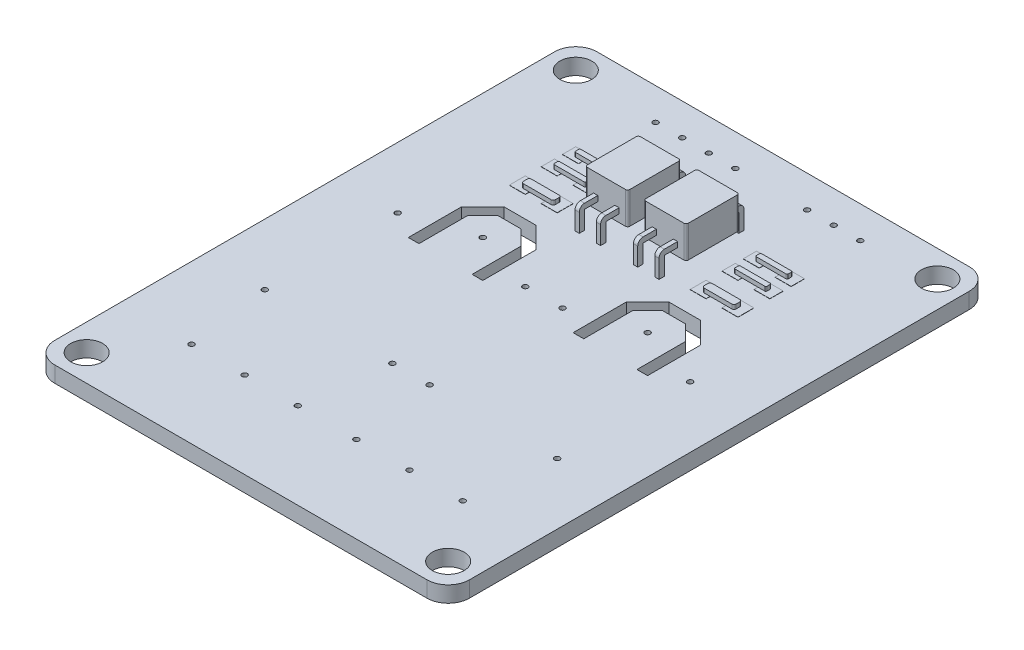
SolidWorks part; units mm, degrees
ref_plane "Ön Düzlem" through (0, 0, 0) normal (0, 0, 1) x (1, 0, 0)
ref_plane "Üst Düzlem" through (0, 0, 0) normal (0, 1, 0) x (1, 0, 0)
ref_plane "Sağ Düzlem" through (0, 0, 0) normal (1, 0, 0) x (0, 0, -1)
sketch "Çizim1" plane through (0, 0, 0) normal (0, 1, 0) x (1, 0, 0)
  line L0 (0, 0) -> (0, 25.5) construction
  line L1 (-17.5, 25.5) -> (17.5, 25.5)
  line L2 (-19.5, 23.5) -> (-19.5, -23.5)
  line L3 (-17.5, -25.5) -> (17.5, -25.5)
  line L4 (19.5, 23.5) -> (19.5, -23.5)
  line L5 (-19.5, 25.5) -> (19.5, -25.5) construction
  line L6 (-19.5, -25.5) -> (19.5, 25.5) construction
  line L7 (0, 25.5) -> (0, 0) construction
  line L8 (0, 0) -> (19.5, 0) construction
  line L9 (-13.75, 25.5) -> (-13.75, -25.5) construction
  line L10 (-19.5, -9.5) -> (19.5, -9.5) construction
  line L11 (-19.5, 3) -> (19.5, 3) construction
  line L12 (-1.75, 25.5) -> (-1.75, -25.5) construction
  line L13 (-19.5, 5) -> (19.5, 5) construction
  line L14 (-7.75, 5) -> (-7.75, -25.5) construction
  line L15 (-19.5, -17.39) -> (19.5, -17.39) construction
  line L16 (-11.25, 6.5) -> (-9.25, 8.5)
  line L17 (-9.25, 8.5) -> (-6.25, 8.5)
  line L18 (-11.25, 6.5) -> (-11.25, 1.5)
  line L20 (-4.25, 6.5) -> (-4.25, 1.5)
  line L21 (-11.25, 8.5) -> (-4.25, 1.5) construction
  line L22 (-11.25, 1.5) -> (-4.25, 8.5) construction
  line L24 (-5.25, 6.0858) -> (-5.25, 1.5)
  line L26 (-8.8358, 7.5) -> (-6.6642, 7.5)
  line L27 (-10.25, 6.0858) -> (-8.8358, 7.5)
  line L28 (-10.25, 6.0858) -> (-10.25, 1.5)
  line L30 (-11.25, 1.5) -> (-10.25, 1.5)
  line L31 (-5.25, 1.5) -> (-4.25, 1.5)
  line L32 (-6.25, 8.5) -> (-4.25, 6.5)
  line L33 (-6.6642, 7.5) -> (-5.25, 6.0858) construction
  line L34 (-6.25, 8.5) -> (-4.25, 6.5) construction
  line L35 (-6.6642, 7.5) -> (-5.25, 6.0858)
  line L36 (5.25, 1.5) -> (4.25, 1.5)
  line L37 (4.25, 6.5) -> (4.25, 1.5)
  line L38 (5.25, 6.0858) -> (5.25, 1.5)
  line L39 (6.6642, 7.5) -> (5.25, 6.0858)
  line L40 (6.25, 8.5) -> (4.25, 6.5)
  line L41 (8.8358, 7.5) -> (6.6642, 7.5)
  line L42 (9.25, 8.5) -> (6.25, 8.5)
  line L43 (10.25, 6.0858) -> (8.8358, 7.5)
  line L44 (11.25, 6.5) -> (9.25, 8.5)
  line L45 (10.25, 6.0858) -> (10.25, 1.5)
  line L46 (11.25, 6.5) -> (11.25, 1.5)
  line L47 (11.25, 1.5) -> (10.25, 1.5)
  line L48 (-19.5, 22.5) -> (19.5, 22.5) construction
  line L49 (7.75, 5) -> (7.75, 25.5) construction
  arc A0 (17.5, -25.5) -> (19.5, -23.5) centre (17.5, -23.5) ccw
  arc A1 (-19.5, -23.5) -> (-17.5, -25.5) centre (-17.5, -23.5) ccw
  arc A2 (17.5, 25.5) -> (19.5, 23.5) centre (17.5, 23.5) cw
  arc A3 (-17.5, 25.5) -> (-19.5, 23.5) centre (-17.5, 23.5) ccw
  circle A4 centre (-17, 23) radius 1.5
  circle A5 centre (17, 23) radius 1.5
  circle A6 centre (17, -23) radius 1.5
  circle A7 centre (-17, -23) radius 1.5
  circle A8 centre (-13.75, -9.5) radius 0.25
  circle A10 centre (-1.75, -9.5) radius 0.25
  circle A11 centre (-13.75, 3) radius 0.25
  circle A12 centre (-7.75, 5) radius 0.25
  circle A13 centre (-1.75, 3) radius 0.25
  circle A14 centre (13.75, 3) radius 0.25
  circle A15 centre (7.75, 5) radius 0.25
  circle A16 centre (1.75, 3) radius 0.25
  circle A17 centre (1.75, -9.5) radius 0.25
  circle A18 centre (13.75, -9.5) radius 0.25
  circle A19 centre (-7.75, -17.39) radius 0.25
  circle A20 centre (-2.75, -17.39) radius 0.25
  circle A21 centre (-12.75, -17.39) radius 0.25
  circle A22 centre (2.75, -17.39) radius 0.25
  circle A23 centre (7.75, -17.39) radius 0.25
  circle A24 centre (12.75, -17.39) radius 0.25
  circle A25 centre (-1.5, 22.5) radius 0.25
  circle A26 centre (-4, 22.5) radius 0.25
  circle A27 centre (-6.5, 22.5) radius 0.25
  circle A28 centre (-9, 22.5) radius 0.25
  circle A29 centre (7.75, 22.5) radius 0.25
  circle A30 centre (10.25, 22.5) radius 0.25
  circle A31 centre (5.25, 22.5) radius 0.25
  point P0 (0, 0)
  dimension "D3" = 2
  dimension "D4" = 3
  dimension "D6" = 2.5
  dimension "D9" = 0.5
  dimension "D15" = 0.5
  dimension "D16" = 5
  dimension "D17" = 5
  dimension "D24" = 0.5
  dimension "D25" = 1.5
  dimension "D26" = 2.5
  dimension "D27" = 2.5
  dimension "D28" = 2.5
  dimension "D29" = 0.5
  dimension "D30" = 2.5
  dimension "D31" = 2.5
  dimension "D1" = 39
  dimension "D2" = 51
  dimension "D5" = 2.5
  dimension "D7" = 5.75
  dimension "D8" = 16
  dimension "D10" = 12.5
  dimension "D11" = 12
  dimension "D12" = 2
  dimension "D13" = 6
  dimension "D14" = 8.11
  dimension "D18" = 7
  dimension "D19" = 7
  dimension "D21" = 3
  dimension "D20" = 1
extrude "Yükseklik-Ekstrüzyon1" add sketch "Çizim1" along normal blind 1.5
sketch "Çizim2" plane through (0, 1.5, 0) normal (0, 1, 0) x (1, 0, 0)
  line L0 (0, 0) -> (0, 25.5) construction
  line L1 (17.5, 25.5) -> (-17.5, 25.5) construction
  line L2 (-7.75, 8.5) -> (-7.75, 25.5) construction
  line L3 (-6.25, 8.5) -> (-9.25, 8.5) construction
  line L4 (-7.75, 10.5) -> (-19.5, 10.5) construction
  line L5 (-19.5, 23.5) -> (-19.5, -23.5) construction
  line L6 (-7.75, 13.5) -> (-19.5, 13.5) construction
  line L7 (-19.5, 15.5) -> (-7.75, 15.5) construction
  line L8 (-9.25, 8.5) -> (-9.25, 15.5) construction
  line L9 (7.75, 12) -> (6.25, 12)
  line L10 (-7.75, 10.5) -> (-6.25, 10.5)
  line L11 (-7.75, 10.5) -> (-7.75, 12)
  line L12 (-7.75, 12) -> (-6.25, 12)
  line L13 (-6.25, 10.5) -> (-6.25, 12)
  line L14 (-9.25, 10.5) -> (-10.75, 10.5)
  line L15 (-9.25, 10.5) -> (-9.25, 12)
  line L16 (-9.25, 12) -> (-10.75, 12)
  line L17 (-10.75, 10.5) -> (-10.75, 12)
  line L18 (-7.75, 13.5) -> (-6.25, 13.5)
  line L19 (-7.75, 13.5) -> (-7.75, 14.75)
  line L20 (-7.75, 14.75) -> (-6.25, 14.75)
  line L21 (-6.25, 13.5) -> (-6.25, 14.75)
  line L22 (-9.25, 13.5) -> (-10.75, 13.5)
  line L23 (-9.25, 13.5) -> (-9.25, 14.75)
  line L24 (-9.25, 14.75) -> (-10.75, 14.75)
  line L25 (-10.75, 13.5) -> (-10.75, 14.75)
  line L26 (-7.75, 15.5) -> (-6.25, 15.5)
  line L27 (-7.75, 15.5) -> (-7.75, 16.75)
  line L28 (-7.75, 16.75) -> (-6.25, 16.75)
  line L29 (-6.25, 15.5) -> (-6.25, 16.75)
  line L30 (-9.25, 15.5) -> (-10.75, 15.5)
  line L31 (-9.25, 15.5) -> (-9.25, 16.75)
  line L32 (-9.25, 16.75) -> (-10.75, 16.75)
  line L33 (-10.75, 15.5) -> (-10.75, 16.75)
  line L34 (6.25, 10.5) -> (6.25, 12)
  line L35 (7.75, 10.5) -> (6.25, 10.5)
  line L36 (7.75, 10.5) -> (7.75, 12)
  line L37 (9.25, 12) -> (10.75, 12)
  line L38 (10.75, 10.5) -> (10.75, 12)
  line L39 (9.25, 10.5) -> (10.75, 10.5)
  line L40 (9.25, 10.5) -> (9.25, 12)
  line L41 (7.75, 14.75) -> (6.25, 14.75)
  line L42 (6.25, 13.5) -> (6.25, 14.75)
  line L43 (7.75, 13.5) -> (6.25, 13.5)
  line L44 (7.75, 13.5) -> (7.75, 14.75)
  line L45 (9.25, 14.75) -> (10.75, 14.75)
  line L46 (10.75, 13.5) -> (10.75, 14.75)
  line L47 (9.25, 13.5) -> (10.75, 13.5)
  line L48 (9.25, 13.5) -> (9.25, 14.75)
  line L49 (7.75, 16.75) -> (6.25, 16.75)
  line L50 (6.25, 15.5) -> (6.25, 16.75)
  line L51 (7.75, 15.5) -> (6.25, 15.5)
  line L52 (7.75, 15.5) -> (7.75, 16.75)
  line L53 (9.25, 16.75) -> (10.75, 16.75)
  line L54 (10.75, 15.5) -> (10.75, 16.75)
  line L55 (9.25, 15.5) -> (10.75, 15.5)
  line L56 (9.25, 15.5) -> (9.25, 16.75)
  dimension "D1" = 2
  dimension "D2" = 3
  dimension "D3" = 2
  dimension "D4" = 1.5
  dimension "D5" = 1.5
  dimension "D6" = 1.5
  dimension "D7" = 1.5
  dimension "D8" = 1.25
  dimension "D9" = 1.5
  dimension "D10" = 1.25
  dimension "D11" = 1.5
  dimension "D12" = 1.25
  dimension "D13" = 1.25
  dimension "D14" = 1.5
  dimension "D15" = 1.5
extrude "Yükseklik-Ekstrüzyon2" add sketch "Çizim2" along normal blind 0.02
sketch "Çizim3" plane through (0, 1.52, 0) normal (0, 1, 0) x (1, 0, 0)
  line L0 (-10.75, 11.25) -> (-6.25, 11.25) construction
  line L1 (-10.75, 12) -> (-10.75, 10.5) construction
  line L2 (-6.25, 10.5) -> (-6.25, 12) construction
  line L3 (-6.25, 11.25) -> (-8.5, 11.25) construction
  line L4 (-8.5, 11.25) -> (-8.5, 16.3146) construction
  line L5 (-10.75, 14.125) -> (-6.25, 14.125) construction
  line L6 (-10.75, 14.75) -> (-10.75, 13.5) construction
  line L7 (-6.25, 13.5) -> (-6.25, 14.75) construction
  line L8 (-10.75, 16.125) -> (-6.25, 16.125) construction
  line L9 (-10.75, 16.75) -> (-10.75, 15.5) construction
  line L10 (-6.25, 15.5) -> (-6.25, 16.75) construction
  line L11 (0, 0) -> (0, 25.4202) construction
  line L12 (-9.9, 16.375) -> (-7.1, 16.375)
  line L13 (-10, 16.275) -> (-10, 15.975)
  line L14 (-9.9, 15.875) -> (-7.1, 15.875)
  line L15 (-7, 16.275) -> (-7, 15.975)
  line L16 (-10, 16.375) -> (-7, 15.875) construction
  line L17 (-10, 15.875) -> (-7, 16.375) construction
  line L18 (-9.9, 14.375) -> (-7.1, 14.375)
  line L19 (-10, 14.275) -> (-10, 13.975)
  line L20 (-9.9, 13.875) -> (-7.1, 13.875)
  line L21 (-7, 14.275) -> (-7, 13.975)
  line L22 (-10, 14.375) -> (-7, 13.875) construction
  line L23 (-10, 13.875) -> (-7, 14.375) construction
  line L24 (-9.8, 11.625) -> (-7.2, 11.625)
  line L25 (-10, 11.425) -> (-10, 11.075)
  line L26 (-9.8, 10.875) -> (-7.2, 10.875)
  line L27 (-7, 11.425) -> (-7, 11.075)
  line L28 (-10, 11.625) -> (-7, 10.875) construction
  line L29 (-10, 10.875) -> (-7, 11.625) construction
  line L30 (9.9, 15.875) -> (7.1, 15.875)
  line L31 (7, 16.275) -> (7, 15.975)
  line L32 (9.9, 16.375) -> (7.1, 16.375)
  line L33 (10, 16.275) -> (10, 15.975)
  line L34 (9.9, 13.875) -> (7.1, 13.875)
  line L35 (7, 14.275) -> (7, 13.975)
  line L36 (9.9, 14.375) -> (7.1, 14.375)
  line L37 (10, 14.275) -> (10, 13.975)
  line L38 (9.8, 10.875) -> (7.2, 10.875)
  line L39 (7, 11.425) -> (7, 11.075)
  line L40 (9.8, 11.625) -> (7.2, 11.625)
  line L41 (10, 11.425) -> (10, 11.075)
  arc A0 (-7.1, 13.875) -> (-7, 13.975) centre (-7.1, 13.975) ccw
  arc A1 (-7.1, 14.375) -> (-7, 14.275) centre (-7.1, 14.275) cw
  arc A2 (-10, 13.975) -> (-9.9, 13.875) centre (-9.9, 13.975) ccw
  arc A3 (-9.9, 14.375) -> (-10, 14.275) centre (-9.9, 14.275) ccw
  arc A4 (-7.1, 15.875) -> (-7, 15.975) centre (-7.1, 15.975) ccw
  arc A5 (-7.1, 16.375) -> (-7, 16.275) centre (-7.1, 16.275) cw
  arc A6 (-10, 15.975) -> (-9.9, 15.875) centre (-9.9, 15.975) ccw
  arc A7 (-9.9, 16.375) -> (-10, 16.275) centre (-9.9, 16.275) ccw
  arc A8 (-7.2, 10.875) -> (-7, 11.075) centre (-7.2, 11.075) ccw
  arc A9 (-7.2, 11.625) -> (-7, 11.425) centre (-7.2, 11.425) cw
  arc A10 (-10, 11.075) -> (-9.8, 10.875) centre (-9.8, 11.075) ccw
  arc A11 (-9.8, 11.625) -> (-10, 11.425) centre (-9.8, 11.425) ccw
  arc A12 (7.1, 15.875) -> (7, 15.975) centre (7.1, 15.975) cw
  arc A13 (7.1, 16.375) -> (7, 16.275) centre (7.1, 16.275) ccw
  arc A14 (10, 15.975) -> (9.9, 15.875) centre (9.9, 15.975) cw
  arc A15 (9.9, 16.375) -> (10, 16.275) centre (9.9, 16.275) cw
  arc A16 (7.1, 13.875) -> (7, 13.975) centre (7.1, 13.975) cw
  arc A17 (7.1, 14.375) -> (7, 14.275) centre (7.1, 14.275) ccw
  arc A18 (10, 13.975) -> (9.9, 13.875) centre (9.9, 13.975) cw
  arc A19 (9.9, 14.375) -> (10, 14.275) centre (9.9, 14.275) cw
  arc A20 (7.2, 10.875) -> (7, 11.075) centre (7.2, 11.075) cw
  arc A21 (7.2, 11.625) -> (7, 11.425) centre (7.2, 11.425) ccw
  arc A22 (10, 11.075) -> (9.8, 10.875) centre (9.8, 11.075) cw
  arc A23 (9.8, 11.625) -> (10, 11.425) centre (9.8, 11.425) cw
  point P20 (-8.5, 16.125)
  point P25 (-8.5, 14.125)
  dimension "D5" = 0.1
  dimension "D6" = 0.2
  dimension "D1" = 0.5
  dimension "D2" = 3
  dimension "D3" = 0.5
  dimension "D4" = 0.75
extrude "Yükseklik-Ekstrüzyon3" add sketch "Çizim3" along normal blind 0.4
ref_plane "Düzlem2" through (0, 2.5, 0) normal (0, 1, 0) x (1, 0, 0)
sketch "Çizim5" plane through (0, 2.5, 0) normal (0, 1, 0) x (1, 0, 0)
  line L0 (0, 0) -> (0, 27.9522) construction
  line L1 (-10, 14.125) -> (0, 14.125) construction
  line L2 (-10, 14.275) -> (-10, 13.975) construction
  line L3 (4.55, 11.625) -> (0.95, 11.625)
  line L4 (-4.55, 16.625) -> (-0.95, 16.625)
  line L5 (-4.75, 16.425) -> (-4.75, 11.825)
  line L6 (-4.55, 11.625) -> (-0.95, 11.625)
  line L7 (-0.75, 16.425) -> (-0.75, 11.825)
  line L8 (-4.75, 16.625) -> (-0.75, 11.625) construction
  line L9 (-4.75, 11.625) -> (-0.75, 16.625) construction
  line L10 (0.75, 16.425) -> (0.75, 11.825)
  line L11 (4.55, 16.625) -> (0.95, 16.625)
  line L12 (4.75, 16.425) -> (4.75, 11.825)
  arc A0 (-0.95, 11.625) -> (-0.75, 11.825) centre (-0.95, 11.825) ccw
  arc A1 (-4.75, 11.825) -> (-4.55, 11.625) centre (-4.55, 11.825) ccw
  arc A2 (-0.95, 16.625) -> (-0.75, 16.425) centre (-0.95, 16.425) cw
  arc A3 (-4.55, 16.625) -> (-4.75, 16.425) centre (-4.55, 16.425) ccw
  arc A4 (0.95, 11.625) -> (0.75, 11.825) centre (0.95, 11.825) cw
  arc A5 (0.95, 16.625) -> (0.75, 16.425) centre (0.95, 16.425) ccw
  arc A6 (4.75, 11.825) -> (4.55, 11.625) centre (4.55, 11.825) cw
  arc A7 (4.55, 16.625) -> (4.75, 16.425) centre (4.55, 16.425) cw
  point P7 (-2.75, 14.125)
  dimension "D4" = 0.2
  dimension "D1" = 5
  dimension "D2" = 4
  dimension "D3" = 0.75
extrude "Yükseklik-Ekstrüzyon4" add sketch "Çizim5" along normal blind 3 separate body
ref_plane "Düzlem3" through (-3.75, 0, 0) normal (-1, 0, 0) x (0, 0, 1)
sketch "Çizim8" plane through (-3.75, 0, 0) normal (-1, 0, 0) x (0, 0, 1)
  line L0 (-14.125, 2.5) -> (-14.125, 0) construction
  line L1 (-16.425, 2.5) -> (-11.825, 2.5) construction
  line L2 (-23.5, 0) -> (23.5, 0) construction
  line L3 (-17.375, 3.2109) -> (-10.375, 3.2109)
  line L5 (-17.875, 0.7988) -> (-17.875, 3.2109)
  line L6 (-17.375, 3.7109) -> (-10.375, 3.7109)
  line L7 (-9.875, 0.7988) -> (-9.875, 3.2109)
  line L8 (-10.375, 0.7988) -> (-9.875, 0.7988)
  line L9 (-17.875, 3.7109) -> (-14.125, 0) construction
  line L10 (-10.375, 0.7988) -> (-10.375, 3.2109)
  line L12 (-17.375, 0.7988) -> (-17.375, 3.2109)
  line L13 (-17.875, 0.7988) -> (-17.375, 0.7988)
  line L14 (-17.875, -3.7109) -> (-17.875, 3.7109) construction
  line L15 (-17.375, -3.2109) -> (-17.375, 3.2109) construction
  line L16 (-14.125, 0) -> (-9.875, 3.7109) construction
  line L17 (-17.875, 3.7109) -> (-9.875, 3.7109) construction
  line L18 (-10.375, -3.2109) -> (-10.375, 3.2109) construction
  line L19 (-9.875, -3.7109) -> (-9.875, 3.7109) construction
  line L21 (-17.375, -3.2109) -> (-10.375, -3.2109) construction
  line L22 (-17.875, -3.7109) -> (-9.875, -3.7109) construction
  arc A0 (-10.375, 3.7109) -> (-9.875, 3.2109) centre (-10.375, 3.2109) cw
  arc A1 (-17.875, 3.2109) -> (-17.375, 3.7109) centre (-17.375, 3.2109) cw
  dimension "D3" = 0.5
  dimension "D1" = 8
  dimension "D2" = 0.5
extrude "Yükseklik-Ekstrüzyon5" add sketch "Çizim8" along normal blind 0.2 and the other way blind 0.2
ref_plane "Düzlem4" through (-1.75, 0, 0) normal (1, 0, 0) x (0, 0, -1)
sketch "Çizim9" plane through (-1.75, 0, 0) normal (1, 0, 0) x (0, 0, -1)
  line L0 (14.125, 2.5) -> (14.125, 0) construction
  line L1 (11.825, 2.5) -> (16.425, 2.5) construction
  line L2 (-23.5, 0) -> (23.5, 0) construction
  line L3 (10.3784, 0.5594) -> (10.3784, 3.2109)
  line L5 (9.8784, 0.5594) -> (9.8784, 3.2109)
  line L6 (10.3784, 3.7109) -> (17.3716, 3.7109)
  line L7 (17.8716, 0.5594) -> (17.8716, 3.2109)
  line L9 (9.8784, 3.7109) -> (14.125, 0) construction
  line L10 (10.3784, 3.2109) -> (17.3716, 3.2109)
  line L11 (17.3716, 0.5594) -> (17.3716, 3.2109)
  line L13 (9.8784, 3.7109) -> (17.8716, 3.7109) construction
  line L14 (17.8716, -3.7109) -> (17.8716, 3.7109) construction
  line L15 (9.8784, -3.7109) -> (9.8784, 3.7109) construction
  line L16 (9.8784, 0.5594) -> (10.3784, 0.5594)
  line L17 (10.3784, -3.2109) -> (10.3784, 3.2109) construction
  line L18 (17.3716, 0.5594) -> (17.8716, 0.5594)
  line L19 (17.3716, -3.2109) -> (17.3716, 3.2109) construction
  line L20 (14.125, 0) -> (17.8716, 3.7109) construction
  line L22 (10.3784, -3.2109) -> (17.3716, -3.2109) construction
  line L24 (9.8784, -3.7109) -> (17.8716, -3.7109) construction
  arc A0 (17.3716, 3.7109) -> (17.8716, 3.2109) centre (17.3716, 3.2109) cw
  arc A1 (9.8784, 3.2109) -> (10.3784, 3.7109) centre (10.3784, 3.2109) cw
  dimension "D2" = 0.5
  dimension "D1" = 0.5
extrude "Yükseklik-Ekstrüzyon6" add sketch "Çizim9" along normal blind 0.2 and the other way blind 0.2
ref_plane "Düzlem5" through (3.75, 0, 0) normal (1, 0, 0) x (0, 0, -1)
sketch "Çizim10" plane through (3.75, 0, 0) normal (1, 0, 0) x (0, 0, -1)
  line L0 (14.125, 2.5) -> (14.125, 0) construction
  line L1 (11.825, 2.5) -> (16.425, 2.5) construction
  line L2 (-23.5, 0) -> (23.5, 0) construction
  line L3 (10.375, 0.6252) -> (10.375, 3.2128)
  line L5 (9.875, 0.6252) -> (9.875, 3.2128)
  line L6 (10.375, 3.7128) -> (17.375, 3.7128)
  line L7 (17.875, 0.6252) -> (17.875, 3.2128)
  line L9 (9.875, 3.7128) -> (14.125, 0) construction
  line L10 (10.375, 3.2128) -> (17.375, 3.2128)
  line L11 (17.375, 0.6252) -> (17.375, 3.2128)
  line L13 (9.875, 3.7128) -> (17.875, 3.7128) construction
  line L14 (17.875, -3.7128) -> (17.875, 3.7128) construction
  line L15 (9.875, -3.7128) -> (9.875, 3.7128) construction
  line L16 (9.875, 0.6252) -> (10.375, 0.6252)
  line L17 (10.375, -3.2128) -> (10.375, 3.2128) construction
  line L18 (14.125, 0) -> (17.875, 3.7128) construction
  line L19 (17.375, 0.6252) -> (17.875, 0.6252)
  line L20 (17.375, -3.2128) -> (17.375, 3.2128) construction
  line L21 (9.875, -3.7128) -> (17.875, -3.7128) construction
  line L22 (10.375, -3.2128) -> (17.375, -3.2128) construction
  arc A0 (17.375, 3.7128) -> (17.875, 3.2128) centre (17.375, 3.2128) cw
  arc A1 (9.875, 3.2128) -> (10.375, 3.7128) centre (10.375, 3.2128) cw
  dimension "D2" = 0.5
  dimension "D1" = 0.5
extrude "Yükseklik-Ekstrüzyon7" add sketch "Çizim10" along normal blind 0.2 and the other way blind 0.2
ref_plane "Düzlem6" through (1.75, 0, 0) normal (-1, 0, 0) x (0, 0, 1)
sketch "Çizim11" plane through (1.75, 0, 0) normal (-1, 0, 0) x (0, 0, 1)
  line L0 (-14.125, 2.5) -> (-14.125, 0) construction
  line L1 (-16.425, 2.5) -> (-11.825, 2.5) construction
  line L2 (-23.5, 0) -> (23.5, 0) construction
  line L3 (-17.375, 0.556) -> (-17.375, 3.2109)
  line L5 (-17.875, 0.556) -> (-17.875, 3.2109)
  line L6 (-17.375, 3.7109) -> (-10.375, 3.7109)
  line L7 (-9.875, 0.556) -> (-9.875, 3.2109)
  line L8 (-10.375, 0.556) -> (-9.875, 0.556)
  line L9 (-17.875, 3.7109) -> (-14.125, 0) construction
  line L10 (-17.375, 3.2109) -> (-10.375, 3.2109)
  line L11 (-10.375, 0.556) -> (-10.375, 3.2109)
  line L13 (-17.875, 3.7109) -> (-9.875, 3.7109) construction
  line L14 (-9.875, -3.7109) -> (-9.875, 3.7109) construction
  line L15 (-17.875, -3.7109) -> (-17.875, 3.7109) construction
  line L16 (-17.875, 0.556) -> (-17.375, 0.556)
  line L17 (-17.375, -3.2109) -> (-17.375, 3.2109) construction
  line L18 (-14.125, 0) -> (-9.875, 3.7109) construction
  line L20 (-10.375, -3.2109) -> (-10.375, 3.2109) construction
  line L21 (-17.875, -3.7109) -> (-9.875, -3.7109) construction
  line L22 (-17.375, -3.2109) -> (-10.375, -3.2109) construction
  arc A0 (-10.375, 3.7109) -> (-9.875, 3.2109) centre (-10.375, 3.2109) cw
  arc A1 (-17.875, 3.2109) -> (-17.375, 3.7109) centre (-17.375, 3.2109) cw
  dimension "D2" = 0.5
  dimension "D1" = 0.5
extrude "Yükseklik-Ekstrüzyon8" add sketch "Çizim11" along normal blind 0.2 and the other way blind 0.2
